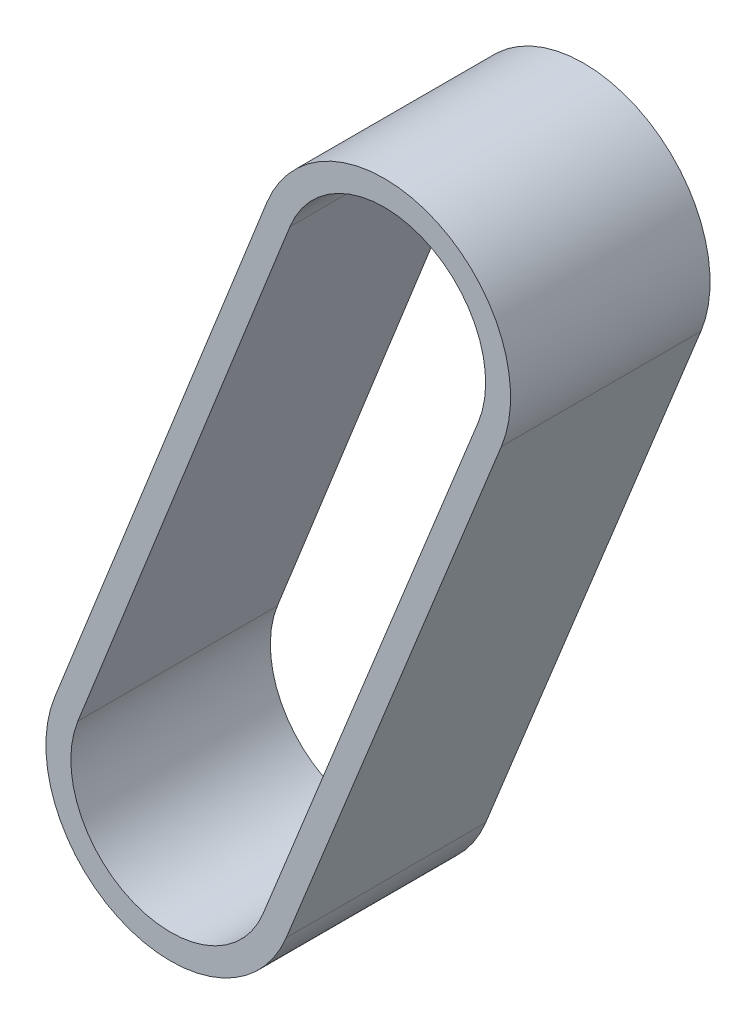
SolidWorks part; units mm, degrees
material "acero"
ref_plane "Alzado" through (0, 0, 0) normal (0, 0, 1) x (1, 0, 0)
ref_plane "Planta" through (0, 0, 0) normal (0, 1, 0) x (1, 0, 0)
ref_plane "Vista lateral" through (0, 0, 0) normal (1, 0, 0) x (0, 0, -1)
sketch "Croquis2" plane through (0, 0, 0) normal (0, 0, 1) x (1, 0, 0)
  line L0 (0, 0) -> (1, 0) construction
  line L1 (0, 0) -> (0, 1) construction
  line L2 (-354.548, 24.136) -> (-367.49, -7.9266)
  line L3 (-380.0231, -2.9097) -> (-367.2668, 29.2272)
  arc A0 (-367.2668, 29.2272) -> (-354.548, 24.136) centre (-360.9, 26.7) cw
  arc A1 (-367.49, -7.9266) -> (-380.0231, -2.9097) centre (-373.7493, -5.4) cw
sketch "Croquis3" plane through (0, 0, 3) normal (0, 0, 1) x (1, 0, 0)
  line L0 (-366.5697, 28.9505) -> (-379.326, -3.1864)
  line L1 (-368.1855, -7.6458) -> (-355.2434, 24.4167)
  line L2 (-367.49, -7.9266) -> (-354.548, 24.136)
  line L3 (-367.2668, 29.2272) -> (-380.0231, -2.9097)
  line L4 (-367.49, -7.9266) -> (-354.548, 24.136) construction
  line L5 (-367.2668, 29.2272) -> (-380.0231, -2.9097) construction
  line L10 (-366.7945, -8.2073) -> (-353.8525, 23.8553)
  line L11 (-367.9639, 29.5039) -> (-380.7202, -2.633)
  arc A0 (-355.2434, 24.4167) -> (-366.5697, 28.9505) centre (-360.9, 26.7) ccw
  arc A1 (-379.326, -3.1864) -> (-368.1855, -7.6458) centre (-373.7493, -5.4) ccw
  arc A2 (-380.0231, -2.9097) -> (-367.49, -7.9266) centre (-373.7493, -5.4) ccw
  arc A3 (-354.548, 24.136) -> (-367.2668, 29.2272) centre (-360.9, 26.7) ccw
  arc A4 (-380.0231, -2.9097) -> (-367.49, -7.9266) centre (-373.7493, -5.4) ccw construction
  arc A5 (-354.548, 24.136) -> (-367.2668, 29.2272) centre (-360.9, 26.7) ccw construction
  arc A10 (-380.7202, -2.633) -> (-366.7945, -8.2073) centre (-373.7493, -5.4) ccw
  arc A11 (-353.8525, 23.8553) -> (-367.9639, 29.5039) centre (-360.9, 26.7) ccw
  dimension "D1" = 0
  dimension "D2" = 0.75
  dimension "D3" = 0.75
  dimension "D4" = 0.75
extrude "Saliente-Extruir1" add sketch "Croquis3" against normal mid plane 12 contours L4 A5 L5 A4 A1 L0 A0 L1
ref_plane "Plano1" through (0, 0, 3) normal (0, 0, 1) x (1, 0, 0)
sketch "Croquis4" plane through (0, 0, 3) normal (0, 0, 1) x (1, 0, 0)
  line L0 (-360.9, 26.7) -> (-373.7493, -5.4)
  arc A0 (-379.326, -3.1864) -> (-368.1855, -7.6458) centre (-373.7493, -5.4) ccw construction
  arc A1 (-355.2434, 24.4167) -> (-366.5697, 28.9505) centre (-360.9, 26.7) ccw construction
